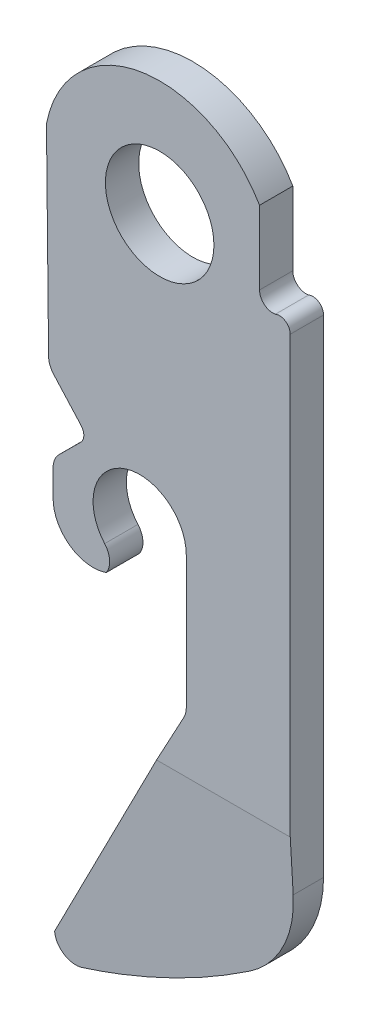
SolidWorks part; units mm, degrees
material "Plain Carbon Steel"
ref_plane "Front Plane" through (0, 0, 0) normal (0, 0, 1) x (1, 0, 0)
ref_plane "Top Plane" through (0, 0, 0) normal (0, 1, 0) x (1, 0, 0)
ref_plane "Right Plane" through (0, 0, 0) normal (1, 0, 0) x (0, 0, -1)
sketch "Sketch1" plane through (0, 0, 0) normal (0, 0, 1) x (1, 0, 0)
  line L0 (20.2608, 45.5867) -> (101.3038, 45.5867) construction
  line L1 (70.2324, 59.1771) -> (70.2324, 40.5971)
  line L2 (60.9327, 61.4779) -> (61.017, 53.5511)
  line L3 (69.0607, 62.8524) -> (69.0607, 60.0535)
  line L5 (61.017, 53.5511) -> (62.2535, 52.1737)
  line L6 (62.2373, 51.6094) -> (61.4119, 50.7898)
  line L7 (61.1867, 50.2491) -> (61.1867, 49.2331)
  line L9 (66.2667, 49.8935) -> (66.2667, 44.6977)
  line L10 (66.2667, 44.6611) -> (60.7803, 34.5011)
  line L12 (66.2667, 44.6977) -> (66.2667, 44.6611)
  arc A1 (69.0607, 60.0535) -> (69.6631, 59.5544) centre (69.5687, 60.0535) ccw
  arc A2 (70.2324, 59.1771) -> (69.6631, 59.5544) centre (69.8227, 59.1771) ccw
  arc A4 (62.2373, 51.6094) -> (62.2535, 52.1737) centre (61.9487, 51.9001) ccw
  arc A5 (61.4119, 50.7898) -> (61.1867, 50.2491) centre (61.9487, 50.2491) ccw
  arc A7 (63.2149, 47.7949) -> (63.153, 48.72) centre (62.5805, 48.2171) ccw
  arc A8 (66.2667, 49.8935) -> (63.153, 48.72) centre (64.4887, 49.8935) ccw
  arc A10 (60.7803, 34.5011) -> (61.7816, 33.7776) centre (61.5423, 34.5011) ccw
  arc A11 (68.3552, 37.0351) -> (70.2324, 40.5971) centre (65.9144, 40.5971) ccw
  arc A12 (61.7816, 33.7776) -> (68.3552, 37.0351) centre (53.5667, 58.6164) ccw
  arc A13 (69.0607, 62.8524) -> (60.9327, 61.4779) centre (65.2507, 60.6631) ccw
  arc A14 (61.1867, 49.2331) -> (63.2149, 47.7949) centre (62.7107, 49.2331) ccw
  point P3 (0, 0)
  point P5 (69.9437, 59.6474)
  point P6 (0, 0)
  point P17 (0, 0)
  point P25 (0, 0)
  point P26 (0, 0)
  point P27 (0, 0)
  point P28 (61.8763, 50.5066)
  point P31 (0, 0)
  point P32 (0, 0)
  point P35 (0, 0)
  point P38 (0, 0)
  point P39 (61.1867, 35.2631)
  point P40 (0, 0)
  point P46 (0, 0)
  point P49 (60.7248, 34.6218)
  point P50 (0, 0)
  point P51 (0, 0)
  point P52 (0, 0)
  point P53 (69.8227, 59.6471)
  point P54 (69.5687, 59.6471)
  point P55 (0, 0)
  point P56 (69.5687, 59.6471)
  point P57 (0, 0)
  point P58 (0, 0)
  point P59 (69.5687, 59.6471)
  point P60 (69.7185, 59.6471)
  point P61 (69.6444, 59.6528)
  point P62 (0, 0)
  point P63 (0, 0)
  point P64 (0, 0)
  point P65 (66.5123, 60.4254)
  point P66 (0, 0)
  point P67 (0, 0)
  point P68 (66.9787, 45.0989)
  point P69 (0, 0)
  point P70 (0, 0)
  point P71 (66.5877, 44.5775)
  point P72 (0, 0)
  point P73 (0, 0)
  point P74 (0, 0)
  point P75 (0, 0)
  dimension "D1" = 4.3942
  dimension "D4" = 0.762
  dimension "D6" = 4.318
  dimension "D7" = 1.486
  dimension "D8" = 3.81
  dimension "D9" = 0.508
  dimension "D10" = 4.318
  dimension "D11" = 20.066
  dimension "D12" = 4.318
  dimension "D13" = 11.684
  dimension "D17" = 16.002
  dimension "D19" = 10.7696
  dimension "D20" = 11.43
  dimension "D21" = 12.446
  dimension "D30" = 7.112
  dimension "D33" = 44.6977
  dimension "D24" = 1.778
  dimension "D29" = 3.302
  dimension "D31" = 2.9972
  dimension "D14" = 26.162
  dimension "D15" = 26.162
  dimension "D18" = 1.016
  dimension "D5" = 4.572
  dimension "D25" = 0.762
  dimension "D27" = 1.524
  dimension "D28" = 0.6096
  dimension "D32" = 0.6096
  dimension "D16" = 3.7084
  dimension "D22" = 10.414
  dimension "D23" = 8.763
  dimension "D26" = 45.5867
extrude "Boss-Extrude1" add sketch "Sketch1" along normal blind 1.27
sketch "Sketch2" plane through (0, 0, 1.27) normal (0, 0, 1) x (1, 0, 0)
  circle A0 centre (65.2507, 60.6631) radius 2.0701
  dimension "D1" = 4.1402
extrude "Cut-Extrude1" cut sketch "Sketch2" against normal through all
fillet "Fillet1" radius 0.762 2 edges at (61.017, 53.5511, 0.635) (66.2667, 44.6611, 0.635)
sketch "Sketch3" plane through (70.2324, 0, 0) normal (1, 0, 0) x (0, 0, -1)
  line L8 (-1.27, 33.7391) -> (-0.762, 33.7391)
  line L9 (-1.27, 33.7391) -> (0, 33.7391) construction
  line L10 (-0.762, 33.7391) -> (-1.27, 42.5639)
  line L11 (-1.27, 40.5971) -> (-1.27, 59.1771) construction
  line L12 (-1.27, 42.5639) -> (-1.27, 33.7391)
  line L13 (0, 33.7776) -> (0, 37.0351) construction
  dimension "D1" = 0.762
  dimension "D2" = 3.295
extrude "Cut-Extrude2" cut sketch "Sketch3" against normal through all
